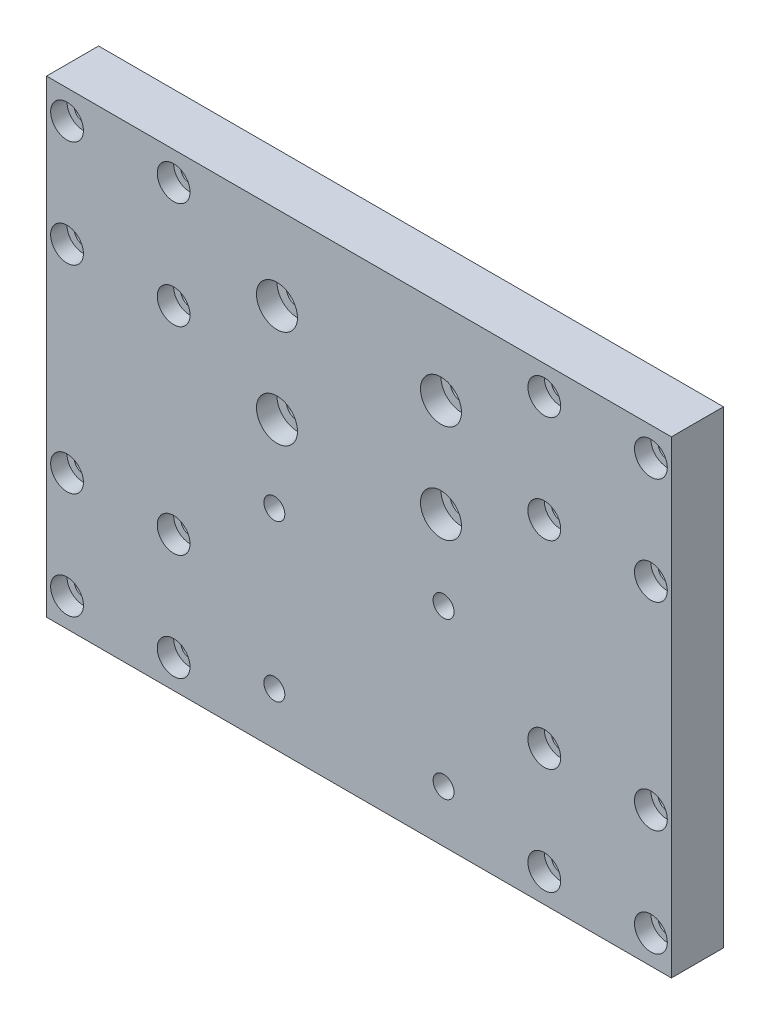
SolidWorks part; units mm, degrees
material "AISI 316 Annealed Stainless Steel Bar (SS)"
ref_plane "Front Plane" through (0, 0, 0) normal (0, 0, 1) x (1, 0, 0)
ref_plane "Top Plane" through (0, 0, 0) normal (0, 1, 0) x (1, 0, 0)
ref_plane "Right Plane" through (0, 0, 0) normal (1, 0, 0) x (0, 0, -1)
sketch "Sketch1" plane through (0, 0, 0) normal (0, 0, 1) x (1, 0, 0)
  line L1 (76.2, -57.15) -> (-76.2, -57.15)
  line L2 (76.2, -57.15) -> (76.2, 57.15)
  line L3 (76.2, 57.15) -> (-76.2, 57.15)
  line L4 (-76.2, -57.15) -> (-76.2, 57.15)
  line L5 (76.2, -57.15) -> (-76.2, 57.15) construction
  line L6 (76.2, 57.15) -> (-76.2, -57.15) construction
  point P0 (0, 0)
  dimension "D1" = 152.4
  dimension "D2" = 114.3
extrude "Boss-Extrude1" add sketch "Sketch1" along normal blind 12.7
hole_wizard "CBORE for #10 Socket Head Cap Screw1" positions "Sketch3" profile "Sketch4" counterbore size "#10" standard "ANSI Inch" end condition through all
sketch "Sketch3" plane through (0, 0, 0) normal (0, 0, -1) x (-1, 0, 0)
  point P0 (-20.6375, -6.35)
  point P2 (20.6375, -6.35)
  point P4 (20.6375, -44.45)
  point P6 (-20.6375, -44.45)
  point P13 (0, 0)
  point P14 (20.6375, -5.4477)
  dimension "D1" = 38.1
  dimension "D2" = 41.275
  dimension "D3" = 20.6375
  dimension "D4" = 6.35
sketch "Sketch4" plane through (20.6375, -6.35, 0) normal (1, 0, 0) x (0, 1, 0)
  line L0 (0, 0) -> (0, 12.7)
  line L1 (0, 12.7) -> (2.5527, 12.7)
  line L3 (2.5527, 12.7) -> (2.5527, 4.826)
  line L4 (2.5527, 4.826) -> (4.7625, 4.826)
  line L5 (4.7625, 4.826) -> (4.7625, 0)
  line L7 (4.7625, 0) -> (0, 0)
  line L11 (0, -6.35) -> (0, 107.95) construction
  dimension "Thru Hole Dia." = 5.1054
  dimension "Thru Hole Depth" = 12.7
  dimension "C'Bore Dia." = 9.525
  dimension "C'Bore Depth" = 4.826
hole_wizard "CBORE for M4 SHCS1" positions "Sketch5" profile "Sketch6" counterbore size "M4" standard "ANSI Metric" end condition through all
sketch "Sketch5" plane through (0, 0, 12.7) normal (0, 0, 1) x (1, 0, 0)
  line L0 (-76.2, -57.15) -> (76.2, -57.15) construction
  line L1 (-76.2, 57.15) -> (-76.2, -57.15) construction
  point P0 (-71.2, -50.15)
  point P2 (-45.2, -50.15)
  point P4 (-45.2, -24.15)
  point P6 (-71.2, -24.15)
  dimension "D1" = 26
  dimension "D2" = 26
  dimension "D3" = 7
  dimension "D4" = 5
sketch "Sketch6" plane through (-71.2, -50.15, 12.7) normal (1, 0, 0) x (0, -1, 0)
  line L0 (0, 0) -> (0, 12.7)
  line L1 (0, 12.7) -> (2.25, 12.7)
  line L3 (2.25, 12.7) -> (2.25, 4)
  line L4 (2.25, 4) -> (4, 4)
  line L5 (4, 4) -> (4, 0)
  line L7 (4, 0) -> (0, 0)
  line L11 (0, -6.35) -> (0, 107.95) construction
  dimension "Thru Hole Dia." = 4.5
  dimension "Thru Hole Depth" = 12.7
  dimension "C'Bore Dia." = 8
  dimension "C'Bore Depth" = 4
mirror "Mirror1" about plane through (0, 0, 0) normal (0, 1, 0) of "CBORE for M4 SHCS1"
mirror "Mirror2" about plane through (0, 0, 0) normal (1, 0, 0) of "Mirror1", "CBORE for M4 SHCS1"
hole_wizard "CBORE for M5 SHCS1" positions "Sketch7" profile "Sketch8" counterbore size "M5" standard "ANSI Metric" end condition through all
sketch "Sketch7" plane through (0, 0, 12.7) normal (0, 0, 1) x (1, 0, 0)
  point P0 (-20, 36.7)
  point P2 (20, 36.7)
  point P4 (20, 12.7)
  point P6 (-20, 12.7)
  point P10 (20, 13.6594)
  dimension "D1" = 40
  dimension "D2" = 24
  dimension "D3" = 20
  dimension "D4" = 12.7
sketch "Sketch8" plane through (-20, 36.7, 12.7) normal (1, 0, 0) x (0, -1, 0)
  line L0 (0, 0) -> (0, 12.7)
  line L1 (0, 12.7) -> (2.75, 12.7)
  line L3 (2.75, 12.7) -> (2.75, 5)
  line L4 (2.75, 5) -> (5, 5)
  line L5 (5, 5) -> (5, 0)
  line L7 (5, 0) -> (0, 0)
  line L11 (0, -6.35) -> (0, 107.95) construction
  dimension "Thru Hole Dia." = 5.5
  dimension "Thru Hole Depth" = 12.7
  dimension "C'Bore Dia." = 10
  dimension "C'Bore Depth" = 5
equation "\"D3@Sketch3\"=\"D2@Sketch3\"/2"
equation "\"D3@Sketch7\"=\"D1@Sketch7\"/2"
